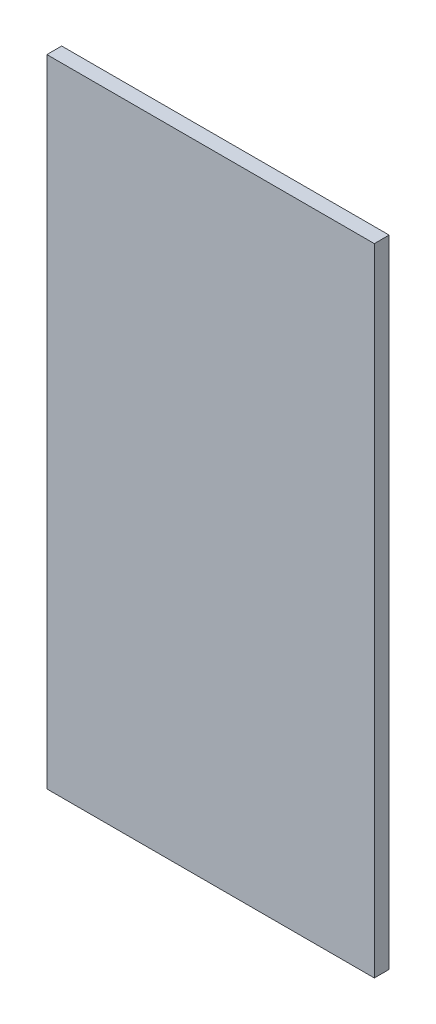
SolidWorks part; units mm, degrees
ref_plane "Front Plane" through (0, 0, 0) normal (0, 0, 1) x (1, 0, 0)
ref_plane "Top Plane" through (0, 0, 0) normal (0, 1, 0) x (1, 0, 0)
ref_plane "Right Plane" through (0, 0, 0) normal (1, 0, 0) x (0, 0, -1)
sketch "Sketch1" plane through (0, 0, 0) normal (0, 0, 1) x (1, 0, 0)
  line L1 (199, -386.5) -> (-199, -386.5)
  line L2 (199, -386.5) -> (199, 386.5)
  line L3 (199, 386.5) -> (-199, 386.5)
  line L4 (-199, -386.5) -> (-199, 386.5)
  line L5 (199, -386.5) -> (-199, 386.5) construction
  line L6 (199, 386.5) -> (-199, -386.5) construction
  point P0 (0, 0)
  dimension "D1" = 773
  dimension "D2" = 398
extrude "Boss-Extrude1" add sketch "Sketch1" along normal blind 18
equation "\"H_DSP\"=18"
equation "\"D1@Boss-Extrude1\"=\"H_DSP\""
